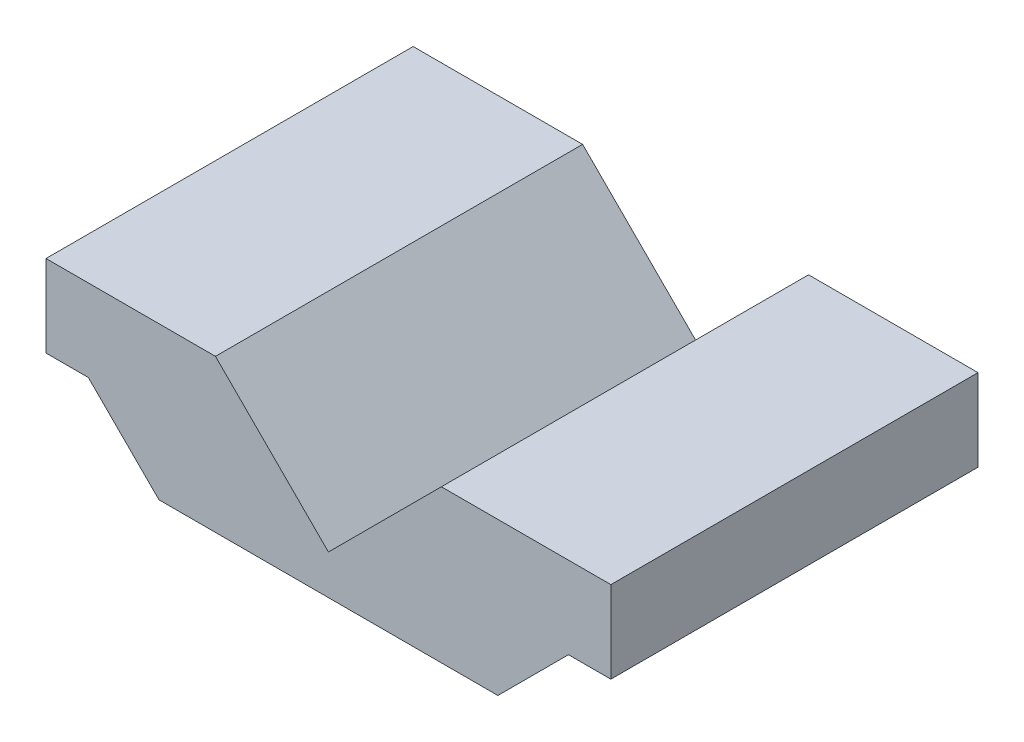
SolidWorks part; units mm, degrees
ref_plane "Alzado" through (0, 0, 0) normal (0, 0, 1) x (1, 0, 0)
ref_plane "Planta" through (0, 0, 0) normal (0, 1, 0) x (1, 0, 0)
ref_plane "Vista lateral" through (0, 0, 0) normal (1, 0, 0) x (0, 0, -1)
sketch "Sketch1" plane through (0, 0, 0) normal (0, 0, 1) x (1, 0, 0)
  line L0 (0, 0) -> (0, 35.3136) construction
  line L1 (-30, 0) -> (30, 0)
  line L2 (30, 0) -> (42.5, 12.5)
  line L3 (42.5, 12.5) -> (50, 12.5)
  line L4 (50, 12.5) -> (50, 27)
  line L5 (50, 27) -> (20, 27)
  line L6 (20, 27) -> (0, 7)
  line L7 (-20, 27) -> (0, 7)
  line L8 (-50, 27) -> (-20, 27)
  line L9 (-50, 12.5) -> (-50, 27)
  line L10 (-42.5, 12.5) -> (-50, 12.5)
  line L11 (-30, 0) -> (-42.5, 12.5)
  dimension "D1" = 50
  dimension "D2" = 20
  dimension "D3" = 45
  dimension "D4" = 30
  dimension "D5" = 12.5
  dimension "D6" = 12.5
  dimension "D7" = 27
extrude "Boss-Extrude1" add sketch "Sketch1" along normal mid plane 65
hole_wizard "Taladro roscado M86" positions "Croquis13" profile "Croquis12" tap size "M8" standard "ISO"
sketch "Croquis13" plane through (15, -15, 0) normal (0.7071, -0.7071, 0) x (0, 0, -1)
  point P0 (-20, 26.4812)
  point P2 (20, 26.4812)
sketch "Croquis12" plane through (33.725, 3.725, 20) normal (0, 0, 1) x (0.7071, 0.7071, 0)
  line L0 (0, 0) -> (0, 22.0429)
  line L1 (0, 22.0429) -> (3.4, 20)
  line L2 (3.4, 20) -> (3.4, 0)
  line L5 (3.4, 0) -> (0, 0)
  line L10 (0, 22.0429) -> (-3.4, 20) construction
  line L11 (0, -6.35) -> (0, 107.95) construction
  dimension "Diámetro de perforador para roscar" = 6.8
  dimension "Profundidad de perforador para roscar" = 20
  dimension "Ángulo de perforador" = 118
cosmetic thread "Rosca de taladro9" parameters "D1"=16, "D2"=8
cosmetic thread "Rosca de taladro10" parameters "D1"=16, "D2"=8
mirror "Simetría3" about plane through (0, 0, 0) normal (1, 0, 0) of "Taladro roscado M86"
